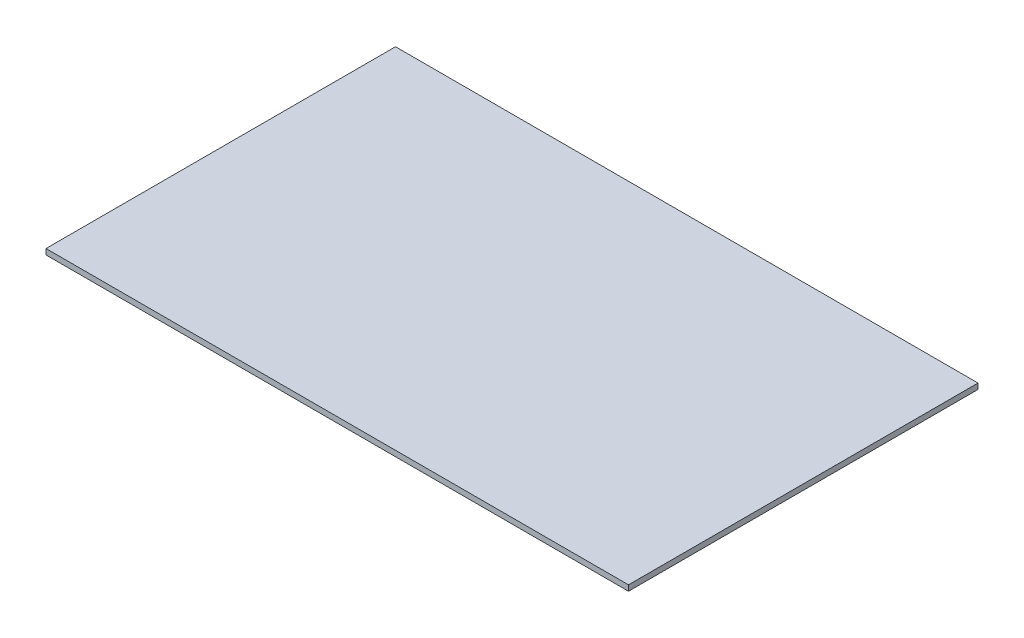
SolidWorks part; units mm, degrees
ref_plane "Front Plane" through (0, 0, 0) normal (0, 0, 1) x (1, 0, 0)
ref_plane "Top Plane" through (0, 0, 0) normal (0, 1, 0) x (1, 0, 0)
ref_plane "Right Plane" through (0, 0, 0) normal (1, 0, 0) x (0, 0, -1)
sketch "Sketch1" plane through (0, 0, 0) normal (0, 1, 0) x (1, 0, 0)
  line L1 (62.5, -37.5) -> (-62.5, -37.5)
  line L2 (62.5, -37.5) -> (62.5, 37.5)
  line L3 (62.5, 37.5) -> (-62.5, 37.5)
  line L4 (-62.5, -37.5) -> (-62.5, 37.5)
  line L5 (62.5, -37.5) -> (-62.5, 37.5) construction
  line L6 (62.5, 37.5) -> (-62.5, -37.5) construction
  point P0 (0, 0)
  dimension "D1" = 125
  dimension "D2" = 75
extrude "Boss-Extrude1" add sketch "Sketch1" along normal blind 1.2
